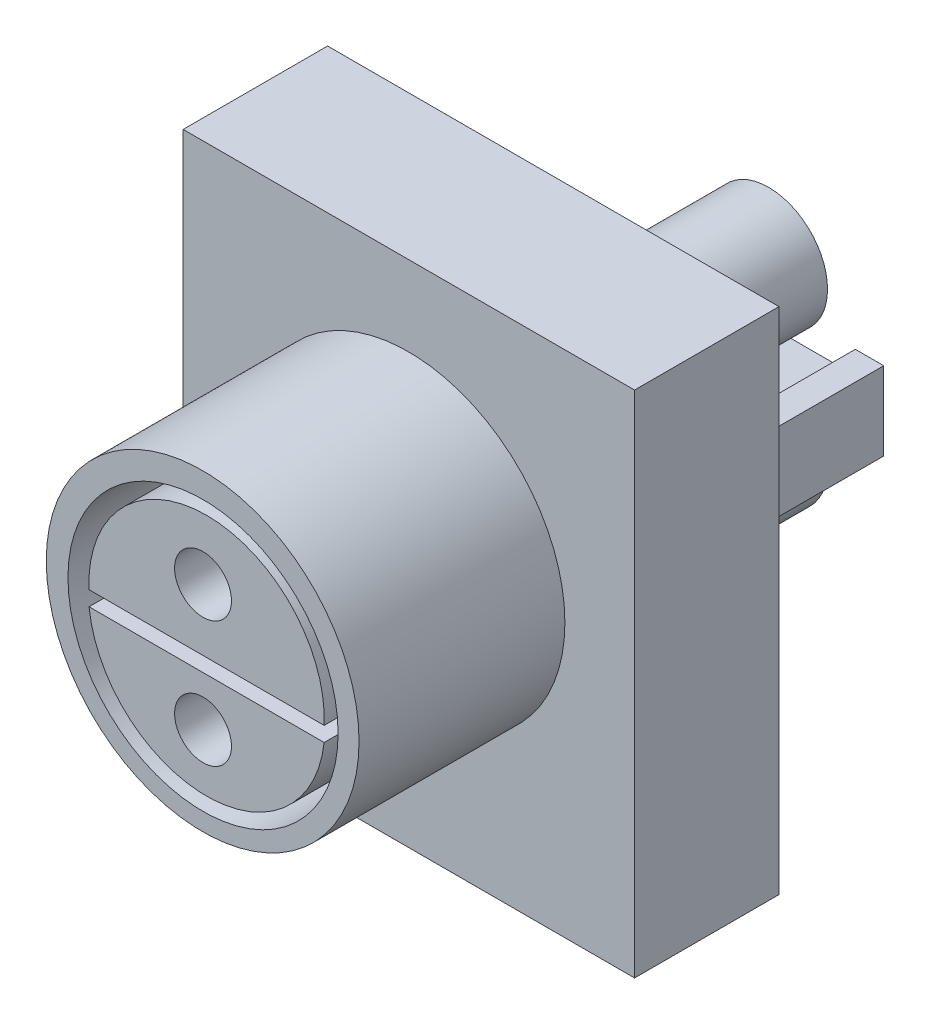
SolidWorks part; units mm, degrees
ref_plane "Front Plane" through (0, 0, 0) normal (0, 0, 1) x (1, 0, 0)
ref_plane "Top Plane" through (0, 0, 0) normal (0, 1, 0) x (1, 0, 0)
ref_plane "Right Plane" through (0, 0, 0) normal (1, 0, 0) x (0, 0, -1)
sketch "Sketch1" plane through (0, 0, 0) normal (0, 0, 1) x (1, 0, 0)
  line L1 (15.875, -17.907) -> (-15.875, -17.907)
  line L2 (15.875, -17.907) -> (15.875, 17.907)
  line L3 (15.875, 17.907) -> (-15.875, 17.907)
  line L4 (-15.875, -17.907) -> (-15.875, 17.907)
  line L5 (15.875, -17.907) -> (-15.875, 17.907) construction
  line L6 (15.875, 17.907) -> (-15.875, -17.907) construction
  point P0 (0, 0)
  dimension "D1" = 31.75
  dimension "D2" = 35.814
extrude "Boss-Extrude1" add sketch "Sketch1" along normal blind 10.16
sketch "Sketch3" plane through (0, 0, 10.16) normal (0, 0, 1) x (1, 0, 0)
  circle A0 centre (-0.0248, 1.2891) radius 11
  dimension "D1" = 22
extrude "Boss-Extrude2" add sketch "Sketch3" along normal blind 14.478
sketch "Sketch4" plane through (0, 0, 0) normal (0, 0, -1) x (-1, 0, 0)
  line L1 (8, -2.75) -> (-8, -2.75)
  line L2 (8, -2.75) -> (8, 2.75)
  line L3 (8, 2.75) -> (-8, 2.75)
  line L4 (-8, -2.75) -> (-8, 2.75)
  line L5 (8, -2.75) -> (-8, 2.75) construction
  line L6 (8, 2.75) -> (-8, -2.75) construction
  point P0 (0, 0)
  dimension "D1" = 16
  dimension "D2" = 5.5
extrude "Boss-Extrude3" add sketch "Sketch4" along normal blind 15.24
sketch "Sketch5" plane through (0, 0, 24.638) normal (0, 0, 1) x (1, 0, 0)
  line L0 (-8.0158, 0) -> (8.5189, 0)
  line L1 (-8.0158, 1.0397) -> (8.5189, 1.0397)
  circle A0 centre (0, 1.0397) radius 9.5
  arc A1 (-8.0158, 1.0397) -> (8.5189, 1.0397) centre (0.2515, 1.4303) cw
  arc A2 (-8.0158, 0) -> (8.5189, 0) centre (0.2515, 0.9136) ccw
  dimension "D1" = 19
extrude "Cut-Extrude1" cut sketch "Sketch5" against normal blind 8.5
sketch "Sketch6" plane through (0, 0, 24.638) normal (0, 0, 1) x (1, 0, 0)
  circle A0 centre (0, 5.3662) radius 2
  dimension "D1" = 4
extrude "Cut-Extrude2" cut sketch "Sketch6" against normal blind 8.5
sketch "Sketch7" plane through (0, 0, 24.638) normal (0, 0, 1) x (1, 0, 0)
  circle A0 centre (0, -3.488) radius 2
  dimension "D1" = 4
extrude "Cut-Extrude3" cut sketch "Sketch7" against normal blind 8.5
sketch "Sketch8" plane through (0, 0, -15.24) normal (0, 0, -1) x (-1, 0, 0)
  line L0 (-6, 2.75) -> (-6, 1.15)
  line L1 (8, 2.75) -> (-8, 2.75) construction
  line L2 (-6, 1.15) -> (6, 1.15)
  line L3 (6, 1.15) -> (6, 2.75)
  line L4 (8, 2.75) -> (-8, 2.75) construction
  line L5 (6, 2.75) -> (-6, 2.75)
  line L6 (-8, 2.75) -> (-8, -2.75) construction
  line L8 (8, -2.75) -> (8, 2.75) construction
  dimension "D1" = 1.6
  dimension "D2" = 2
  dimension "D3" = 2
extrude "Cut-Extrude4" cut sketch "Sketch8" against normal blind 15.15
sketch "Sketch10" plane through (0, 0, -15.24) normal (0, 0, -1) x (-1, 0, 0)
  line L0 (-6, -2.75) -> (-6, -1.15)
  line L1 (-8, -2.75) -> (8, -2.75) construction
  line L2 (-6, -1.15) -> (6, -1.15)
  line L3 (6, -1.15) -> (6, -2.75)
  line L4 (-8, -2.75) -> (8, -2.75) construction
  line L5 (6, -2.75) -> (-6, -2.75)
  line L6 (-8, 2.75) -> (-8, -2.75) construction
  line L7 (8, -2.75) -> (8, 2.75) construction
  dimension "D1" = 2
  dimension "D2" = 2
  dimension "D3" = 1.6
extrude "Cut-Extrude5" cut sketch "Sketch10" against normal blind 15.15
sketch "Sketch12" plane through (0, 0, 0) normal (0, 0, -1) x (-1, 0, 0)
  circle A0 centre (0, 5.5236) radius 4.1358
extrude "Boss-Extrude4" add sketch "Sketch12" along normal blind 15.15
sketch "Sketch13" plane through (0, 0, -15.15) normal (0, 0, -1) x (-1, 0, 0)
  circle A0 centre (0, 5.6281) radius 3
  circle A1 centre (0, 5.5236) radius 4.1358 construction
  dimension "D1" = 6
extrude "Cut-Extrude6" cut sketch "Sketch13" against normal blind 15.15
sketch "Sketch14" plane through (0, 0, 0) normal (0, 0, -1) x (-1, 0, 0)
  circle A0 centre (0, -5.3662) radius 4.135
extrude "Boss-Extrude5" add sketch "Sketch14" along normal blind 15.15
sketch "Sketch15" plane through (0, 0, -15.15) normal (0, 0, -1) x (-1, 0, 0)
  circle A0 centre (0, -5.3662) radius 3
  dimension "D1" = 6
extrude "Cut-Extrude7" cut sketch "Sketch15" against normal blind 15.15
